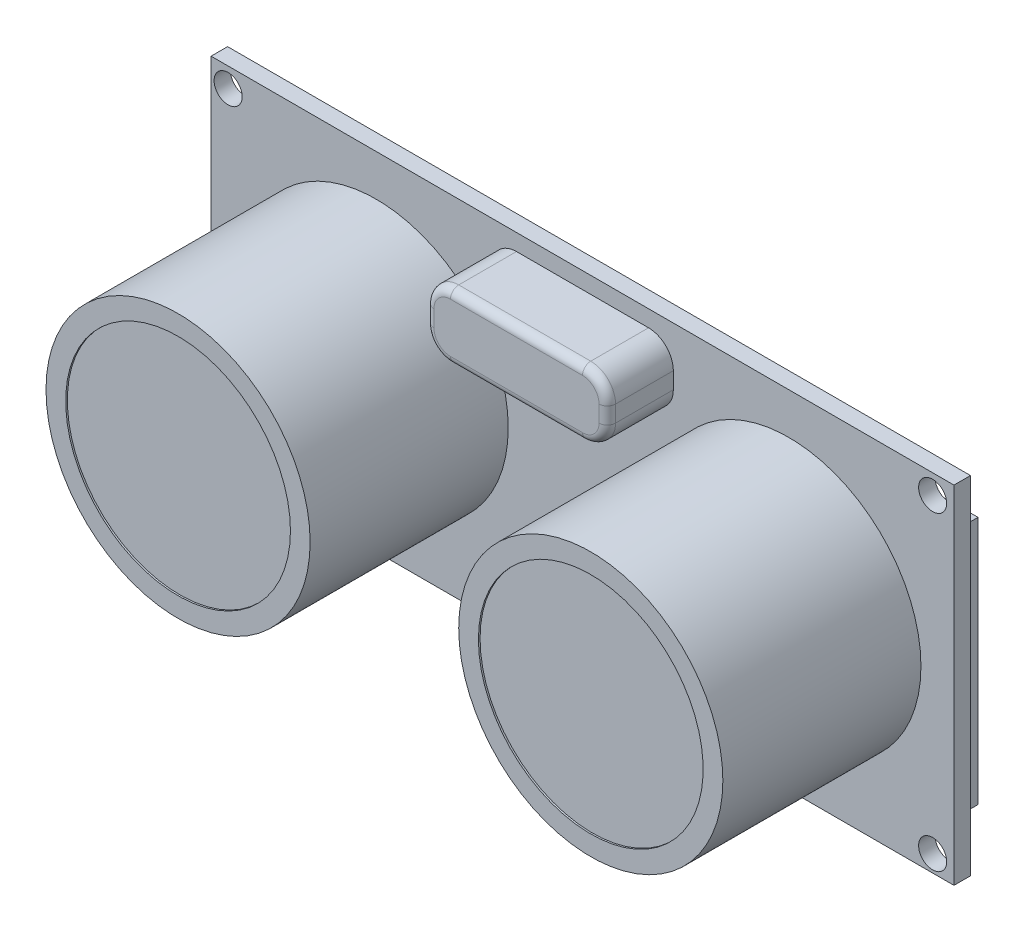
SolidWorks part; units mm, degrees
ref_plane "Front" through (0, 0, 0) normal (0, 0, 1) x (1, 0, 0)
ref_plane "Top" through (0, 0, 0) normal (0, 1, 0) x (1, 0, 0)
ref_plane "Right" through (0, 0, 0) normal (1, 0, 0) x (0, 0, -1)
sketch "Skizze2" plane through (0, 0, 0) normal (0, 0, 1) x (1, 0, 0)
  line L1 (-22.5, -10.5) -> (22.5, -10.5)
  line L2 (-22.5, -10.5) -> (-22.5, 10.5)
  line L3 (-22.5, 10.5) -> (22.5, 10.5)
  line L4 (22.5, -10.5) -> (22.5, 10.5)
  line L5 (-22.5, -10.5) -> (22.5, 10.5) construction
  line L6 (-22.5, 10.5) -> (22.5, -10.5) construction
  point P1 (0, 0)
  dimension "D1" = 45
  dimension "D2" = 21
extrude "Aufsatz-Linear austragen1" add sketch "Skizze2" along normal blind 1
sketch "Skizze3" plane through (0, 0, 1) normal (0, 0, 1) x (1, 0, 0)
  line L0 (-22.5, 10.5) -> (-22.5, -10.5) construction
  line L1 (0, 10.5) -> (0, -10.5) construction
  line L2 (22.5, 10.5) -> (-22.5, 10.5) construction
  line L3 (-22.5, -10.5) -> (22.5, -10.5) construction
  circle A0 centre (-12.5, 0) radius 8
  circle A1 centre (12.5, 0) radius 8
  dimension "D1" = 16
  dimension "D2" = 10
extrude "Aufsatz-Linear austragen2" add sketch "Skizze3" along normal blind 12 contours A0 | A1
sketch "Skizze4" plane through (0, 0, 13) normal (0, 0, 1) x (1, 0, 0)
  line L0 (-12.5, 8) -> (-12.5, -8) construction
  line L1 (-20.5, 0) -> (-4.5, 0) construction
  line L2 (0, 10.5) -> (0, -10.5) construction
  line L3 (22.5, 10.5) -> (-22.5, 10.5) construction
  line L4 (-22.5, -10.5) -> (22.5, -10.5) construction
  circle A1 centre (-12.5, 0) radius 8 construction
  circle A2 centre (-12.5, 0) radius 8 construction
  circle A3 centre (-12.5, 0) radius 6.8073
  circle A4 centre (12.5, 0) radius 6.8073
extrude "Schnitt-Linear austragen1" cut sketch "Skizze4" against normal blind 0.1
ref_plane "Ebene1" through (-22.5, 10.5, 1) normal (-1, 0, 0) x (0, 0, 1)
sketch "Skizze7" plane through (0, 0, 1) normal (0, 0, 1) x (1, 0, 0)
  line L0 (0, 10.5) -> (0, -10.5) construction
  line L1 (22.5, 10.5) -> (-22.5, 10.5) construction
  line L2 (-22.5, -10.5) -> (22.5, -10.5) construction
  line L4 (5.5, 9.5) -> (-5.5, 9.5)
  line L5 (5.5, 9.5) -> (5.5, 5.5)
  line L6 (5.5, 5.5) -> (-5.5, 5.5)
  line L7 (-5.5, 9.5) -> (-5.5, 5.5)
  line L8 (5.5, 9.5) -> (-5.5, 5.5) construction
  line L9 (5.5, 5.5) -> (-5.5, 9.5) construction
  point P6 (0, 7.5)
  dimension "D1" = 4
  dimension "D2" = 20
  dimension "D3" = 11
  dimension "D4" = 1
extrude "Aufsatz-Linear austragen3" add sketch "Skizze7" along normal blind 4
fillet "Verrundung1" radius 1.5 4 edges at (-5.5, 5.5, 3) (-5.5, 9.5, 3) (5.5, 5.5, 3) (5.5, 9.5, 3)
fillet "Verrundung2" radius 0.5 8 edges at (-5.5, 7.5, 5) (-5.0607, 9.0607, 5) (0, 9.5, 5) (5.0607, 9.0607, 5) (5.5, 7.5, 5) (5.0607, 5.9393, 5) (-5.0607, 5.9393, 5) (0, 5.5, 5)
hole_wizard "Durchgangsloch für M1.61" positions "Skizze8" profile "Skizze9" hole size "M1.6" standard "DIN" end condition through all
sketch "Skizze8" plane through (0, 0, 1) normal (0, 0, 1) x (1, 0, 0)
  point P0 (-21.4686, 9.3113)
  point P2 (-21.4686, -9.4821)
  point P4 (21.2078, -9.4821)
  point P6 (21.2078, 9.3113)
sketch "Skizze9" plane through (-21.4686, 9.3113, 1) normal (1, 0, 0) x (0, -1, 0)
  line L0 (0, 0) -> (0, 1)
  line L1 (0, 1) -> (0.85, 1)
  line L2 (0.85, 1) -> (0.85, 0)
  line L5 (0.85, 0) -> (0, 0)
  line L11 (0, -6.35) -> (0, 107.95) construction
  dimension "Bohrerdurchmesser" = 1.7
  dimension "Bohrungstiefe" = 1
sketch "Skizze10" plane through (0, 0, 0) normal (0, 0, -1) x (-1, 0, 0)
  line L1 (-21.9555, 7.5347) -> (21.9555, 7.5347)
  line L2 (-21.9555, 7.5347) -> (-21.9555, -7.5347)
  line L3 (-21.9555, -7.5347) -> (21.9555, -7.5347)
  line L4 (21.9555, 7.5347) -> (21.9555, -7.5347)
  line L5 (-21.9555, 7.5347) -> (21.9555, -7.5347) construction
  line L6 (-21.9555, -7.5347) -> (21.9555, 7.5347) construction
  point P0 (0, 0)
extrude "Aufsatz-Linear austragen4" add sketch "Skizze10" along normal blind 1
sketch "Skizze11" plane through (0, 0, 0) normal (0, 0, -1) x (-1, 0, 0)
  line L0 (0, 10.5) -> (0, -10.5) construction
  line L1 (-22.5, 10.5) -> (22.5, 10.5) construction
  line L2 (22.5, -10.5) -> (-22.5, -10.5) construction
  line L4 (-5.5, -8) -> (5.5, -8)
  line L5 (-5.5, -8) -> (-5.5, -10.5)
  line L6 (-5.5, -10.5) -> (5.5, -10.5)
  line L7 (5.5, -8) -> (5.5, -10.5)
  line L8 (-5.5, -8) -> (5.5, -10.5) construction
  line L9 (-5.5, -10.5) -> (5.5, -8) construction
  point P6 (0, -9.25)
  dimension "D1" = 11
  dimension "D2" = 2.5
extrude "Aufsatz-Linear austragen6" add sketch "Skizze11" along normal blind 2 separate body
fillet "Verrundung5" radius 0.3 12 edges at (5.5, -9.25, 0) (5.5, -10.5, -1) (0, -10.5, 0) (-5.5, -10.5, -1) (-5.5, -9.25, 0) (-5.5, -8, -1) (5.5, -8, -1) (0, -8, 0) (0, -10.5, -2) (5.5, -9.25, -2) (0, -8, -2) (-5.5, -9.25, -2)
